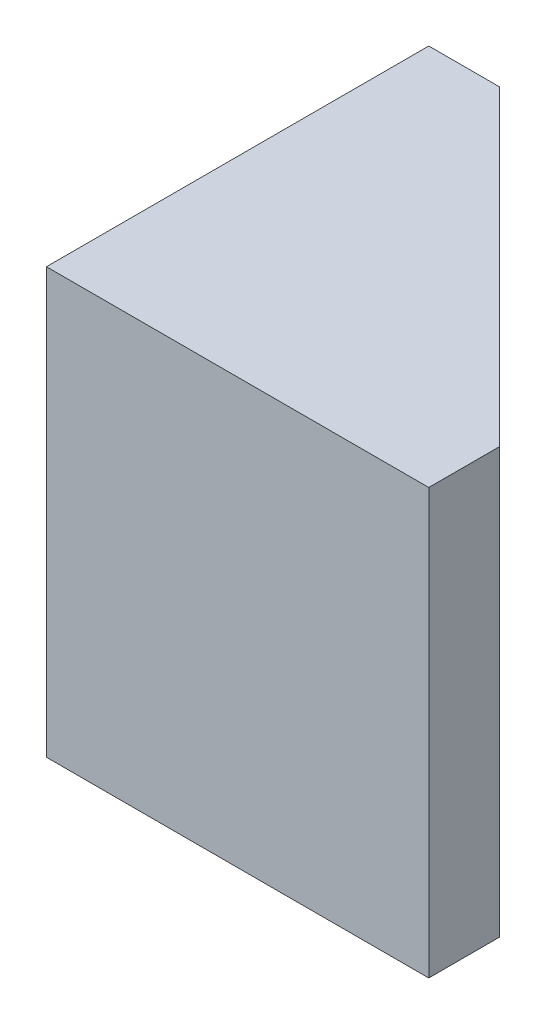
SolidWorks part; units mm, degrees
ref_plane "Front Plane" through (0, 0, 0) normal (0, 0, 1) x (1, 0, 0)
ref_plane "Top Plane" through (0, 0, 0) normal (0, 1, 0) x (1, 0, 0)
ref_plane "Right Plane" through (0, 0, 0) normal (1, 0, 0) x (0, 0, -1)
sketch "Sketch1" plane through (0, 0, 0) normal (0, 1, 0) x (1, 0, 0)
  line L0 (0, 0) -> (0, 32)
  line L1 (0, 32) -> (32, 0)
  line L2 (32, 0) -> (0, 0)
  dimension "D1" = 32
extrude "Boss-Extrude1" add sketch "Sketch1" along normal blind 30
sketch "Sketch2" plane through (0, 30, 0) normal (0, 1, 0) x (1, 0, 0)
  line L0 (0, 27) -> (5, 27)
  line L1 (0, 32) -> (0, 0) construction
  line L2 (32, 0) -> (0, 32) construction
  line L3 (0, 0) -> (5.7722, 5.7722) construction
  line L4 (0, 0) -> (32, 0) construction
  line L5 (0, 27) -> (0, 32)
  line L6 (0, 32) -> (5, 27)
  line L7 (27, 0) -> (32, 0)
  line L8 (27, 0) -> (27, 5)
  line L9 (32, 0) -> (27, 5)
  dimension "D1" = 45
  dimension "D2" = 27
extrude "Cut-Extrude1" cut sketch "Sketch2" against normal through all
